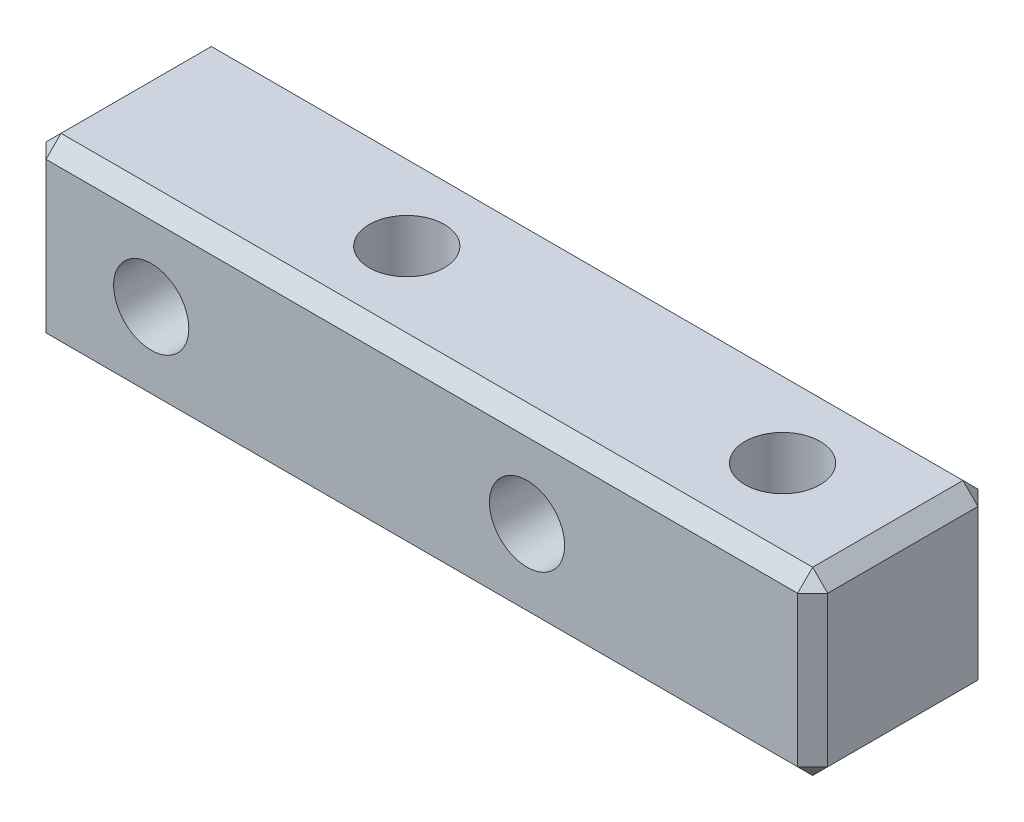
SolidWorks part; units mm, degrees
material "6063-T5"
ref_plane "前视基准面" through (0, 0, 0) normal (0, 0, 1) x (1, 0, 0)
ref_plane "上视基准面" through (0, 0, 0) normal (0, 1, 0) x (1, 0, 0)
ref_plane "右视基准面" through (0, 0, 0) normal (1, 0, 0) x (0, 0, -1)
other "Configuration Table"
sketch "草图1" plane through (0, 0, 0) normal (0, 0, 1) x (1, 0, 0)
  line L1 (-13, -3) -> (13, -3)
  line L2 (-13, -3) -> (-13, 3)
  line L3 (-13, 3) -> (13, 3)
  line L4 (13, -3) -> (13, 3)
  line L5 (-13, -3) -> (13, 3) construction
  line L6 (-13, 3) -> (13, -3) construction
  point P0 (0, 0)
  dimension "D1" = 6
  dimension "D2" = 26
extrude "凸台-拉伸1" add sketch "草图1" along normal blind 6
chamfer "倒角1" distance 0.5 angle 45 12 edges at (13, 0, 0) (13, -3, 3) (0, -3, 0) (-13, -3, 3) (-13, 0, 0) (0, -3, 6) (-13, 0, 6) (13, 0, 6) (13, 3, 3) (0, 3, 6) (-13, 3, 3) (0, 3, 0)
sketch "草图2" plane through (0, 0, 6) normal (0, 0, 1) x (1, 0, 0)
  line L0 (-13, -2.5) -> (-13, 2.5) construction
  circle A0 centre (-9, 0) radius 1.525
  circle A1 centre (3.5, 0) radius 1.525
  dimension "D2" = 3.05
  dimension "D1" = 12.5
  dimension "D3" = 4
hole_wizard "M3 螺纹孔1" positions "3D草图1" profile "草图3" tap size "M3" standard "KS" end condition through all
sketch3d "3D草图1"
  point P0 (-9, 0, 6)
  point P3 (3.5, 0, 6)
sketch "草图3" plane through (-9, 0, 6) normal (1, 0, 0) x (0, -1, 0)
  line L0 (0, 0) -> (0, 6)
  line L1 (0, 6) -> (1.25, 6)
  line L2 (1.25, 6) -> (1.25, 0)
  line L5 (1.25, 0) -> (0, 0)
  line L11 (0, -6.35) -> (0, 107.95) construction
  dimension "通孔螺纹孔钻头直径" = 2.5
  dimension "通孔螺纹孔钻头深度" = 6
cosmetic thread "孔螺蚊线1"
cosmetic thread "孔螺蚊线2"
sketch "草图4" plane through (0, 3, 0) normal (0, 1, 0) x (1, 0, 0)
  line L0 (13, -0.5) -> (13, -5.5) construction
  line L1 (12.5, -6) -> (-12.5, -6) construction
  circle A0 centre (-3.5, -3) radius 1.525
  circle A1 centre (9, -3) radius 1.525
  dimension "D1" = 12.5
  dimension "D4" = 3.05
  dimension "D2" = 4
  dimension "D3" = 3
hole_wizard "M3 螺纹孔2" positions "3D草图2" profile "草图5" tap size "M3" standard "KS" end condition through all
sketch3d "3D草图2"
  point P0 (-3.5, 3, 3)
  point P3 (9, 3, 3)
sketch "草图5" plane through (-3.5, 3, 3) normal (1, 0, 0) x (0, 0, 1)
  line L0 (0, 0) -> (0, 6)
  line L1 (0, 6) -> (1.25, 6)
  line L2 (1.25, 6) -> (1.25, 0)
  line L5 (1.25, 0) -> (0, 0)
  line L11 (0, -6.35) -> (0, 107.95) construction
  dimension "通孔螺纹孔钻头直径" = 2.5
  dimension "通孔螺纹孔钻头深度" = 6
cosmetic thread "孔螺蚊线3"
cosmetic thread "孔螺蚊线4"
